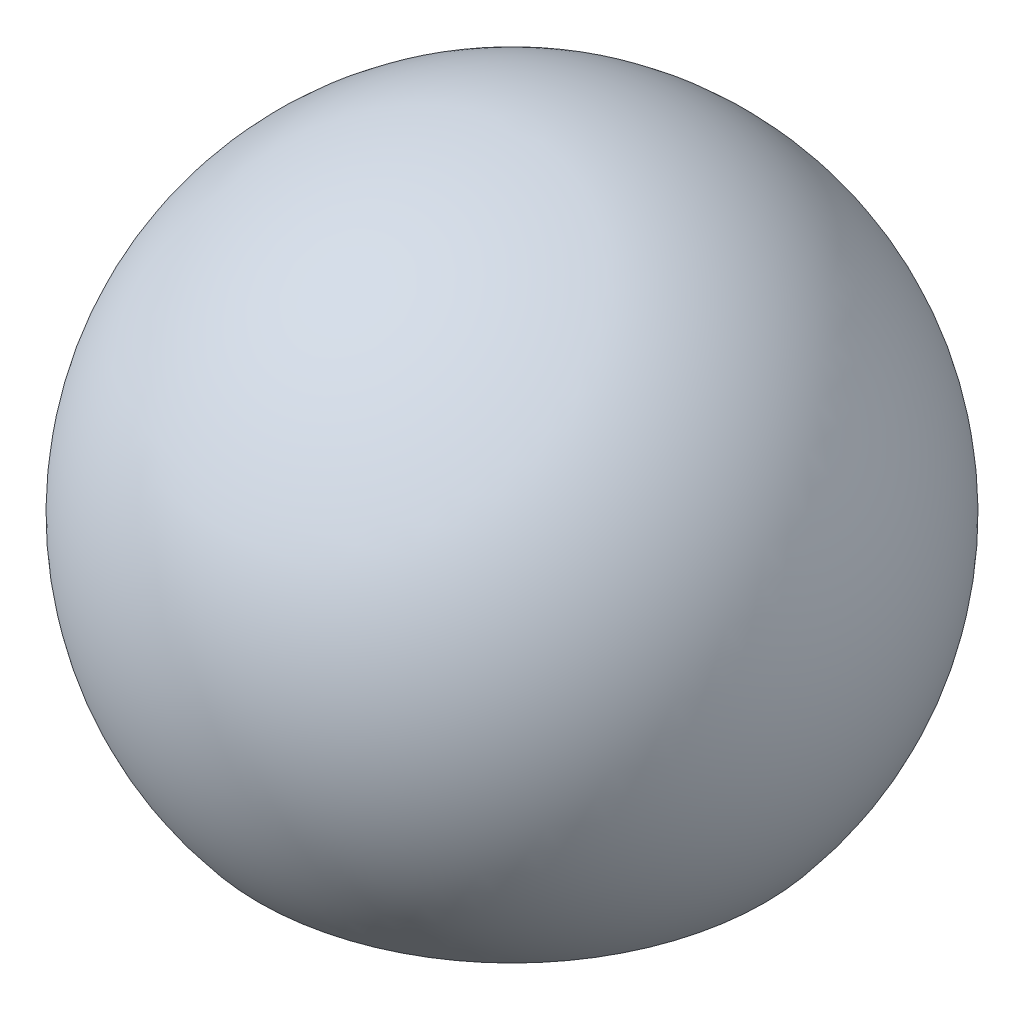
SolidWorks part; units mm, degrees
ref_plane "Front Plane" through (0, 0, 0) normal (0, 0, 1) x (1, 0, 0)
ref_plane "Top Plane" through (0, 0, 0) normal (0, 1, 0) x (1, 0, 0)
ref_plane "Right Plane" through (0, 0, 0) normal (1, 0, 0) x (0, 0, -1)
sketch "Sketch1" plane through (0, 0, 0) normal (0, 0, 1) x (1, 0, 0)
  line L0 (0, 130.2238) -> (0, -83.4161)
  line L1 (0, -83.4161) -> (-100, -83.4161)
  arc A0 (0, 130.2238) -> (-100, -83.4161) centre (0, 0) ccw
revolve "Revolve1" add sketch "Sketch1" angle 360 about L0
